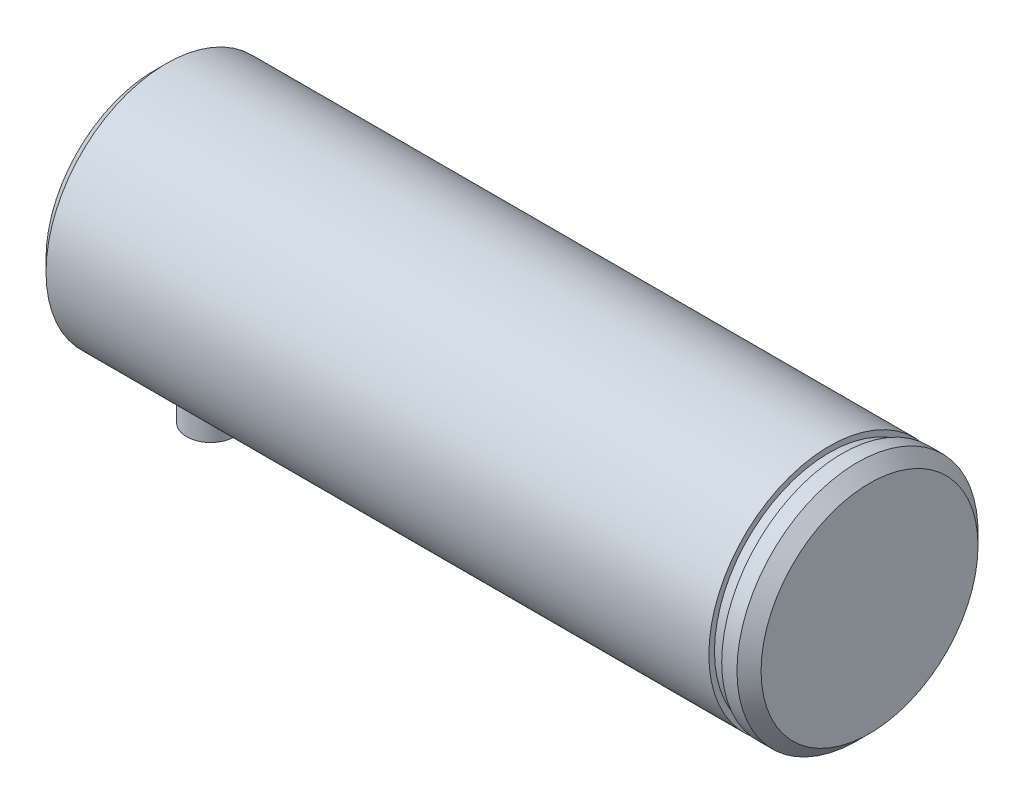
SolidWorks part; units mm, degrees
ref_plane "Front Plane" through (0, 0, 0) normal (0, 0, 1) x (1, 0, 0)
ref_plane "Top Plane" through (0, 0, 0) normal (0, 1, 0) x (1, 0, 0)
ref_plane "Right Plane" through (0, 0, 0) normal (1, 0, 0) x (0, 0, -1)
ref_plane "Plane1" through (0, 0, 0) normal (0, 0, 1) x (1, 0, 0)
sketch "Sketch1" plane through (0, 0, 0) normal (0, 0, 1) x (1, 0, 0)
  line L0 (-44.5, 0) -> (-44.5, 15)
  line L1 (-44.5, 15) -> (39.5, 15)
  line L2 (39.5, 15) -> (39.5, 0)
  line L3 (39.5, 0) -> (-44.5, 0)
  line L4 (39.5, 0) -> (-44.5, 0) construction
revolve "Revolve1" add sketch "Sketch1" angle 360 about L4
ref_plane "Plane2" through (0, 0, 0) normal (0, 0, 1) x (1, 0, 0)
sketch "Sketch2" plane through (0, 0, 0) normal (0, 0, 1) x (1, 0, 0)
  line L0 (-44.5, 13.5) -> (-43, 15)
  line L1 (-43, 15) -> (-44.5, 15)
  line L2 (-44.5, 15) -> (-44.5, 13.5)
  line L3 (77, 0) -> (-77, 0) construction
revolve "Cut-Revolve1" cut sketch "Sketch2" angle 360 about L3
ref_plane "Plane3" through (0, 0, 0) normal (0, 1, 0) x (1, 0, 0)
sketch "Sketch3" plane through (0, 0, 0) normal (0, 1, 0) x (1, 0, 0)
  circle A0 centre (-37.5, 0) radius 3
extrude "Boss-Extrude1" add sketch "Sketch3" against normal blind 21
ref_plane "Plane4" through (0, 0, 0) normal (0, 0, 1) x (1, 0, 0)
sketch "Sketch4" plane through (0, 0, 0) normal (0, 0, 1) x (1, 0, 0)
  line L0 (39.5, 0) -> (39.5, 15)
  line L1 (39.5, 15) -> (44.5, 15)
  line L2 (44.5, 15) -> (44.5, 0)
  line L3 (44.5, 0) -> (39.5, 0)
  line L4 (44.5, 0) -> (39.5, 0) construction
revolve "Revolve2" add sketch "Sketch4" angle 360 about L4
ref_plane "Plane5" through (0, 0, 0) normal (0, 0, 1) x (1, 0, 0)
sketch "Sketch5" plane through (0, 0, 0) normal (0, 0, 1) x (1, 0, 0)
  line L0 (39.5, 14.3) -> (41.1, 14.3)
  line L1 (41.1, 14.3) -> (41.1, 15)
  line L2 (41.1, 15) -> (39.5, 15)
  line L3 (39.5, 15) -> (39.5, 14.3)
  line L4 (77, 0) -> (-77, 0) construction
revolve "Cut-Revolve2" cut sketch "Sketch5" angle 360 about L4
ref_plane "Plane6" through (0, 0, 0) normal (0, 0, 1) x (1, 0, 0)
sketch "Sketch6" plane through (0, 0, 0) normal (0, 0, 1) x (1, 0, 0)
  line L0 (43, 15) -> (44.5, 13.5)
  line L1 (44.5, 13.5) -> (44.5, 15)
  line L2 (44.5, 15) -> (43, 15)
  line L3 (77, 0) -> (-77, 0) construction
revolve "Cut-Revolve3" cut sketch "Sketch6" angle 360 about L3
